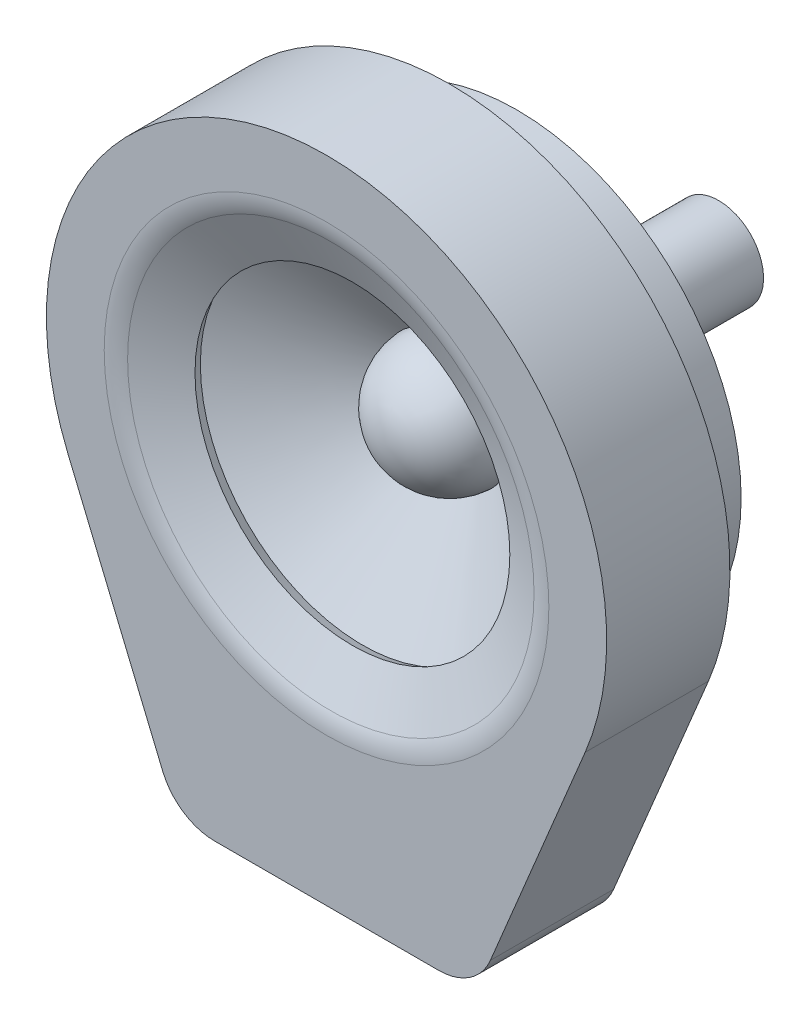
SolidWorks part; units mm, degrees
material "Polyetheretherketone (PEEK)"
ref_plane "Front" through (0, 0, 0) normal (0, 0, 1) x (1, 0, 0)
ref_plane "Top" through (0, 0, 0) normal (0, 1, 0) x (1, 0, 0)
ref_plane "Right" through (0, 0, 0) normal (1, 0, 0) x (0, 0, -1)
sketch "Sketch1" plane through (0, 0, 0) normal (1, 0, 0) x (0, 0, -1)
  line L0 (0, 0) -> (-5.9446, 0) construction
  line L1 (0, 0) -> (12, 0)
  line L3 (12, 0) -> (12, 2)
  line L4 (12, 2) -> (3, 2)
  line L5 (3, 2) -> (3, 10)
  line L6 (3, 10) -> (0, 10)
  line L7 (0, 10) -> (0, 0)
  dimension "D1" = 4
  dimension "D2" = 10
  dimension "D3" = 3
  dimension "D4" = 12
revolve "Revolve1" add sketch "Sketch1" angle 360 about L0
sketch "Sketch2" plane through (0, 0, 0) normal (1, 0, 0) x (0, 0, -1)
  line L0 (0, 0) -> (-2.779, 0) construction
  line L1 (0, 0) -> (-5.9446, 0) construction
  line L2 (0, 2.779) -> (-3.5917, 9)
  line L3 (0, 10) -> (0, -10) construction
  line L4 (-3.5917, 9) -> (-3.5917, 11)
  line L5 (3, 10) -> (0, 10) construction
  arc A0 (-2.779, 0) -> (0, 2.779) centre (0, 0) cw
  dimension "D1" = 30
  dimension "D2" = 1
  dimension "D3" = 2
revolve "Revolve-Thin2" add sketch "Sketch2" angle 360 about L0 wall 0.1
sketch "Sketch4" plane through (0, 0, 0) normal (0, 0, 1) x (1, 0, 0)
  line L0 (0, 0) -> (0, -16) construction
  line L1 (-5.0019, -16) -> (5.0019, -16)
  line L2 (6.8481, -14.7689) -> (11.0776, -4.6137)
  line L3 (-6.8481, -14.7689) -> (-11.0776, -4.6137)
  arc A1 (-6.8481, -14.7689) -> (-5.0019, -16) centre (-5.0019, -14) ccw
  circle A2 centre (0, 0) radius 12
  arc A3 (11.0776, -4.6137) -> (-11.0776, -4.6137) centre (0, 0) ccw
  arc A4 (5.0019, -16) -> (6.8481, -14.7689) centre (5.0019, -14) ccw
  point P9 (-6.3354, -16)
  point P12 (6.3354, -16)
  dimension "D2" = 16
  dimension "D4" = 2
  dimension "D1" = 1
extrude "Extrude-Thin1" add sketch "Sketch4" along normal blind 5 thin
sketch "Sketch5" plane through (0, 0, 5) normal (0, 0, 1) x (1, 0, 0)
  line L3 (-11.5392, -4.8059) -> (-7.3097, -14.9612)
  line L4 (-5.0019, -16.5) -> (5.0019, -16.5)
  line L5 (7.3097, -14.9612) -> (11.5392, -4.8059)
  line L6 (-11.5392, -4.8059) -> (-7.3097, -14.9612)
  line L7 (-5.0019, -16.5) -> (5.0019, -16.5)
  line L8 (7.3097, -14.9612) -> (11.5392, -4.8059)
  arc A3 (11.5392, -4.8059) -> (-11.5392, -4.8059) centre (0, 0) ccw
  arc A4 (-7.3097, -14.9612) -> (-5.0019, -16.5) centre (-5.0019, -14) ccw
  arc A5 (5.0019, -16.5) -> (7.3097, -14.9612) centre (5.0019, -14) ccw
  arc A6 (11.5392, -4.8059) -> (-11.5392, -4.8059) centre (0, 0) ccw
  arc A7 (-7.3097, -14.9612) -> (-5.0019, -16.5) centre (-5.0019, -14) ccw
  arc A8 (5.0019, -16.5) -> (7.3097, -14.9612) centre (5.0019, -14) ccw
  circle A9 centre (0, 0) radius 9.9732
  circle A10 centre (0, 0) radius 9.9732
  dimension "D1" = 0
  dimension "D2" = 1
extrude "Extrude1" add sketch "Sketch5" along normal blind 0.5
sketch "Sketch6" plane through (0, 0, 0) normal (1, 0, 0) x (0, 0, -1)
  line L0 (-5.5, 9.9732) -> (-5.5, 9.4732)
  line L1 (-5.5, 12.5) -> (-5.5, -4.8059) construction
  line L2 (-5.5, 9.4732) -> (-4.3454, 7.0247)
  line L3 (0, 0) -> (-2.0776, 0) construction
  line L4 (0, 0) -> (-5.9446, 0) construction
  dimension "D1" = 0.5
revolve "Revolve-Thin3" add sketch "Sketch6" angle 360 about L3 wall 0.5
fillet "Fillet1" radius 2 1 edges at (-9.4732, 0, 5.5)
